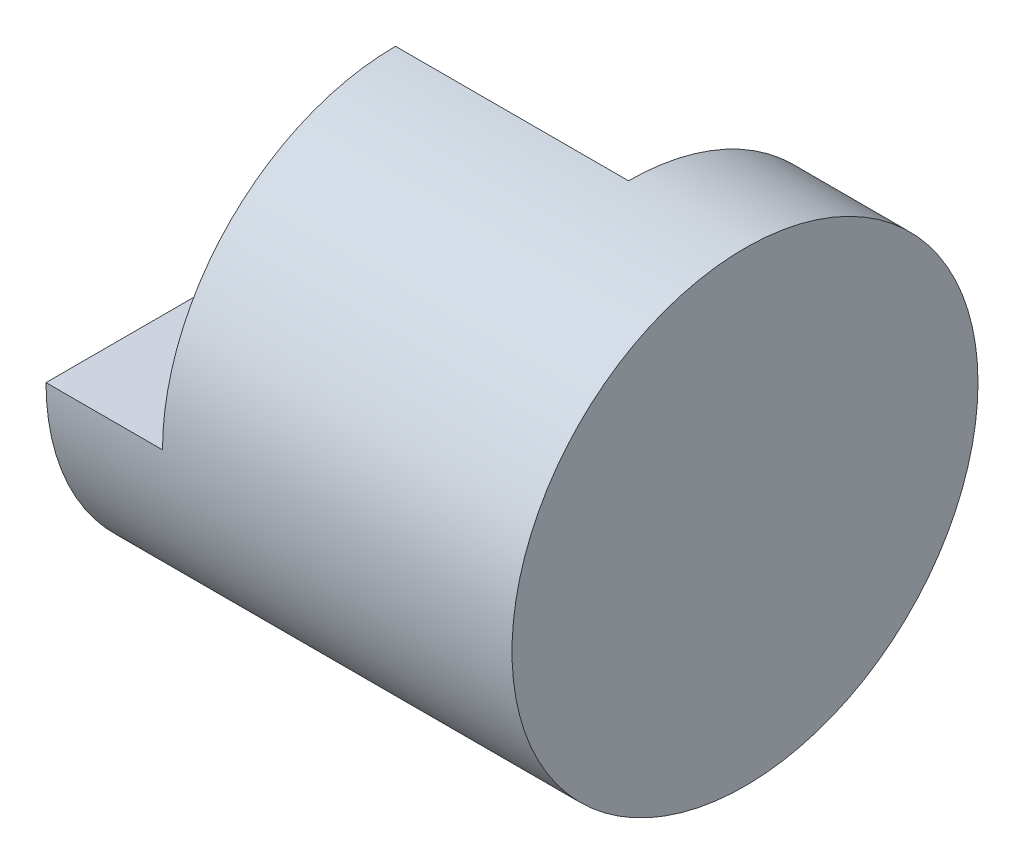
SolidWorks part; units mm, degrees
ref_plane "Front" through (0, 0, 0) normal (0, 0, 1) x (1, 0, 0)
ref_plane "Top" through (0, 0, 0) normal (0, 1, 0) x (1, 0, 0)
ref_plane "Right" through (0, 0, 0) normal (1, 0, 0) x (0, 0, -1)
sketch "Sketch1" plane through (0, 0, 0) normal (1, 0, 0) x (0, 0, -1)
  circle A0 centre (0, 0) radius 2
  dimension "D1" = 4
extrude "Boss-Extrude1" add sketch "Sketch1" along normal mid plane 4
sketch "Sketch3" plane through (0, 0, 0) normal (0, 1, 0) x (1, 0, 0)
  line L0 (-2, 2) -> (-2, -2)
  line L1 (-2, -2) -> (-1, -2)
  line L2 (-2, -2) -> (2, -2) construction
  line L3 (1, -2) -> (1, 0)
  line L4 (1, 0) -> (-1, 0)
  line L6 (2, 2) -> (-2, 2) construction
  line L7 (-1, 2) -> (-2, 2)
  line L8 (1, 0) -> (1, 2)
  line L9 (2, 2) -> (-2, 2) construction
  line L10 (-1, 0) -> (-1, -2)
  line L11 (-1, 2) -> (1, 2)
  dimension "D1" = 1
  dimension "D2" = 3
  dimension "D3" = 2
extrude "Cut-Extrude1" cut sketch "Sketch3" along normal blind 4 contours L11 L7 L0 L1 L10 L4 L8
